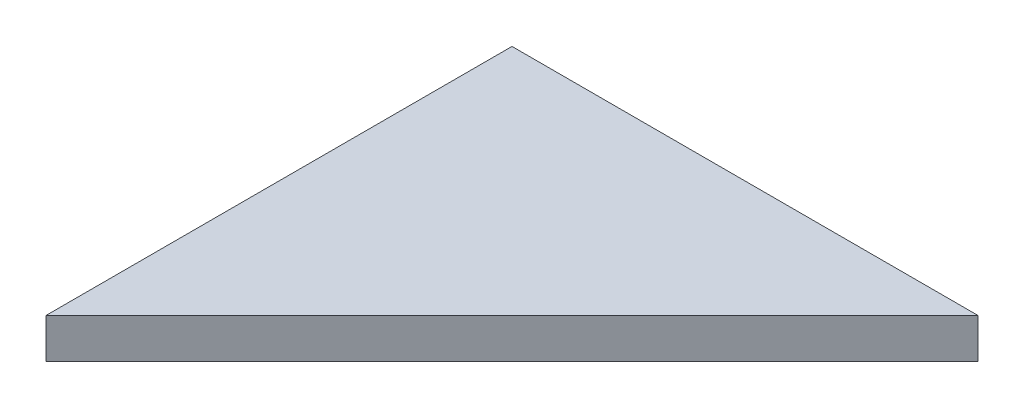
SolidWorks part; units mm, degrees
material "1.0036 (S235JRG1)"
ref_plane "Front Plane" through (0, 0, 0) normal (0, 0, 1) x (1, 0, 0)
ref_plane "Top Plane" through (0, 0, 0) normal (0, 1, 0) x (1, 0, 0)
ref_plane "Right Plane" through (0, 0, 0) normal (1, 0, 0) x (0, 0, -1)
sketch "Sketch1" plane through (0, 0, 0) normal (0, 1, 0) x (1, 0, 0)
  line L0 (0, 0) -> (70, 0)
  line L1 (70, 0) -> (0, -70)
  line L2 (0, -70) -> (0, 0)
  dimension "D1" = 70
extrude "Boss-Extrude1" add sketch "Sketch1" along normal blind 6
